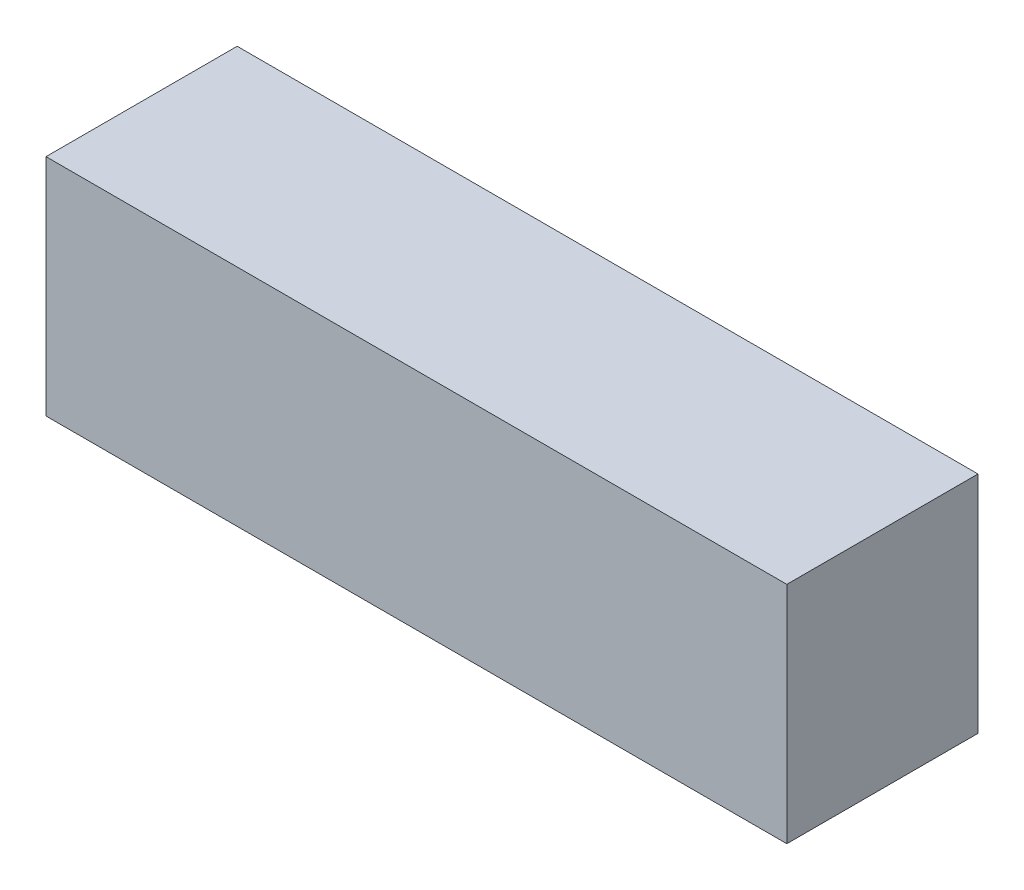
SolidWorks part; units mm, degrees
ref_plane "Plano frontal" through (0, 0, 0) normal (0, 0, 1) x (1, 0, 0)
ref_plane "Plano superior" through (0, 0, 0) normal (0, 1, 0) x (1, 0, 0)
ref_plane "Plano direito" through (0, 0, 0) normal (1, 0, 0) x (0, 0, -1)
sketch "Esboço1" plane through (0, 0, 0) normal (0, 0, 1) x (1, 0, 0)
  line L1 (-87.3047, 28.5621) -> (67.6953, 28.5621)
  line L2 (-87.3047, 28.5621) -> (-87.3047, -18.4379)
  line L3 (-87.3047, -18.4379) -> (67.6953, -18.4379)
  line L4 (67.6953, 28.5621) -> (67.6953, -18.4379)
  dimension "D1" = 155
  dimension "D2" = 47
extrude "Ressalto-extrusão1" add sketch "Esboço1" along normal blind 40
